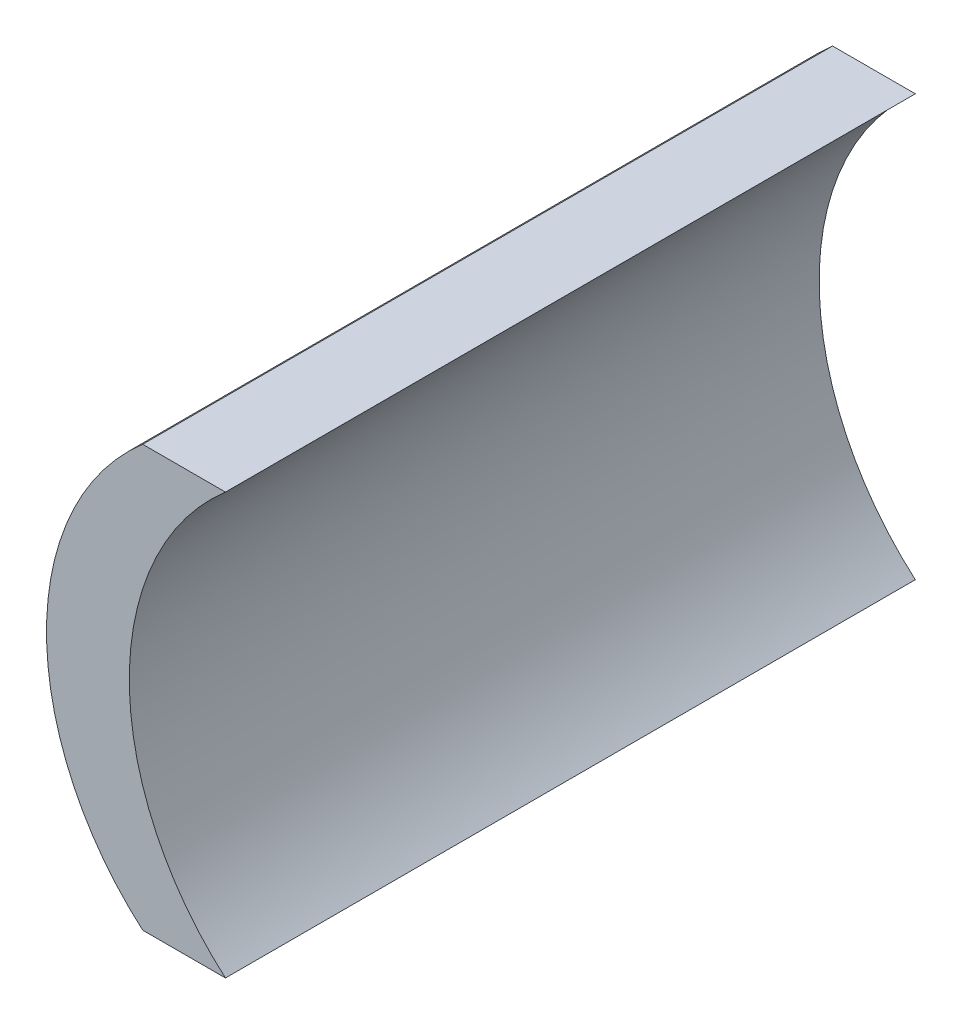
SolidWorks part; units mm, degrees
material "ABS"
ref_plane "Front Plane" through (0, 0, 0) normal (0, 0, 1) x (1, 0, 0)
ref_plane "Top Plane" through (0, 0, 0) normal (0, 1, 0) x (1, 0, 0)
ref_plane "Right Plane" through (0, 0, 0) normal (1, 0, 0) x (0, 0, -1)
sketch "Sketch2" plane through (0, 0, 0) normal (0, 0, 1) x (1, 0, 0)
  line L1 (-26.225, -9.15) -> (26.225, -9.15)
  line L2 (-26.225, -9.15) -> (-26.225, 9.15)
  line L3 (-26.225, 9.15) -> (26.225, 9.15)
  line L4 (26.225, -9.15) -> (26.225, 9.15)
  line L5 (-26.225, -9.15) -> (26.225, 9.15) construction
  line L6 (-26.225, 9.15) -> (26.225, -9.15) construction
  circle A0 centre (0, 0) radius 12.1
  circle A1 centre (-3.6, 0) radius 12.1
  dimension "D1" = 24.2
  dimension "D3" = 24.2
  dimension "D2" = 18.3
  dimension "D4" = 3.6
extrude "Boss-Extrude1" add sketch "Sketch2" along normal blind 30 contours L3 A1 L1 A0
